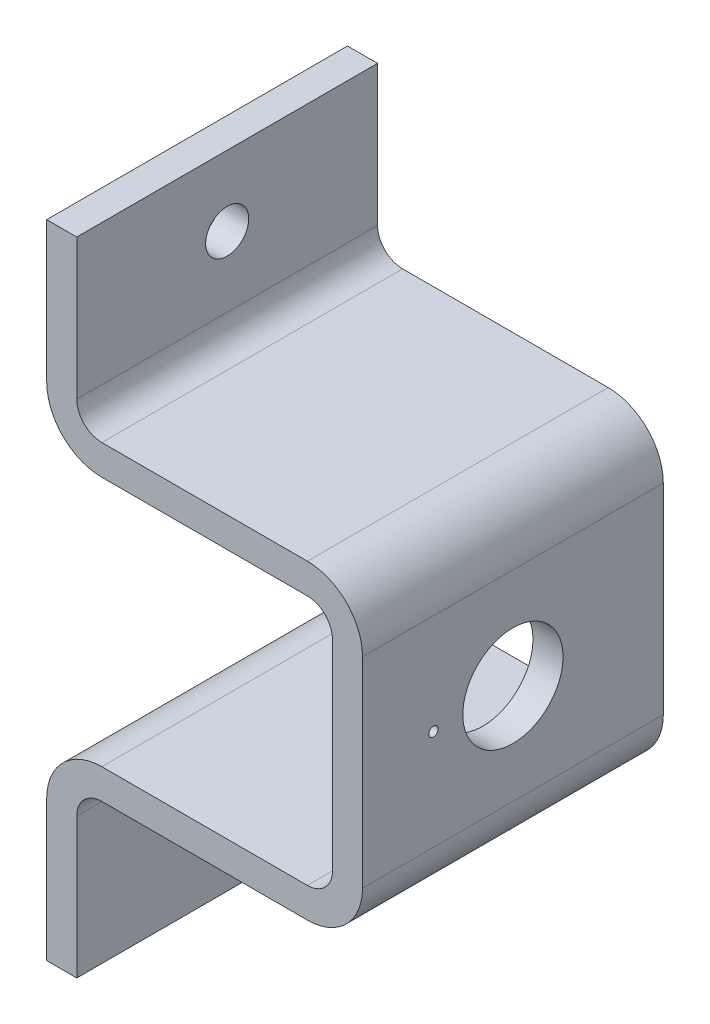
SolidWorks part; units mm, degrees
material "80% - PLA"
ref_plane "Front Plane" through (0, 0, 0) normal (0, 0, 1) x (1, 0, 0)
ref_plane "Top Plane" through (0, 0, 0) normal (0, 1, 0) x (1, 0, 0)
ref_plane "Right Plane" through (0, 0, 0) normal (1, 0, 0) x (0, 0, -1)
sketch "Sketch1" plane through (0, 0, 0) normal (0, 0, 1) x (1, 0, 0)
  line L0 (0, 0) -> (0, 14)
  line L1 (26, 19.5) -> (5.5, 19.5)
  line L2 (28.5, 22) -> (28.5, 42)
  line L3 (26, 44.5) -> (5.5, 44.5)
  line L4 (0, 50) -> (0, 64)
  line L5 (3, 0) -> (3, 14)
  line L6 (5.5, 16.5) -> (26, 16.5)
  line L7 (31.5, 22) -> (31.5, 42)
  line L8 (26, 47.5) -> (5.5, 47.5)
  line L9 (3, 50) -> (3, 64)
  line L10 (0, 0) -> (0, 19.5) construction
  line L11 (0, 19.5) -> (28.5, 19.5) construction
  line L12 (3, 0) -> (3, 16.5) construction
  line L13 (3, 16.5) -> (31.5, 16.5) construction
  line L14 (28.5, 19.5) -> (28.5, 44.5) construction
  line L15 (31.5, 16.5) -> (31.5, 47.5) construction
  line L16 (28.5, 44.5) -> (0, 44.5) construction
  line L17 (31.5, 47.5) -> (3, 47.5) construction
  line L18 (0, 44.5) -> (0, 64) construction
  line L19 (3, 47.5) -> (3, 64) construction
  line L20 (0, 64) -> (3, 64)
  line L21 (3, 0) -> (0, 0)
  arc A0 (0, 14) -> (5.5, 19.5) centre (5.5, 14) cw
  arc A1 (3, 14) -> (5.5, 16.5) centre (5.5, 14) cw
  arc A2 (26, 19.5) -> (28.5, 22) centre (26, 22) ccw
  arc A3 (31.5, 42) -> (26, 47.5) centre (26, 42) ccw
  arc A4 (28.5, 42) -> (26, 44.5) centre (26, 42) ccw
  arc A6 (0, 14) -> (5.5, 19.5) centre (5.5, 14) cw construction
  arc A7 (5.5, 47.5) -> (3, 50) centre (5.5, 50) cw
  arc A8 (5.5, 44.5) -> (0, 50) centre (5.5, 50) cw
  arc A9 (5.5, 44.5) -> (0, 50) centre (5.5, 50) cw construction
  arc A10 (26, 16.5) -> (31.5, 22) centre (26, 22) ccw
  arc A11 (26, 16.5) -> (31.5, 22) centre (26, 22) ccw construction
  arc A12 (31.5, 42) -> (26, 47.5) centre (26, 42) ccw construction
  dimension "D6" = 3
  dimension "D1" = 3
  dimension "D2" = 3
  dimension "D3" = 3
  dimension "D4" = 3
  dimension "D7" = 25.5
  dimension "D8" = 19.5
  dimension "D9" = 19.5
  dimension "D10" = 31
  dimension "D5" = 3
extrude "Boss-Extrude1" add sketch "Sketch1" along normal blind 30
hole_wizard "M4 Clearance Hole1" positions "Sketch3" profile "Sketch2" hole size "M4" standard "ISO"
sketch "Sketch3" plane through (3, 0, 0) normal (1, 0, 0) x (0, 0, -1)
  line L0 (-30, 0) -> (0, 0) construction
  line L1 (0, 0) -> (0, 14) construction
  point P0 (-15, 57)
  point P2 (-15, 7)
  dimension "D1" = 50
  dimension "D2" = 7
  dimension "D3" = 15
sketch "Sketch2" plane through (3, 57, 15) normal (0, 1, 0) x (0, 0, -1)
  line L0 (0, 0) -> (0, 7)
  line L1 (0, 7) -> (2.15, 7)
  line L2 (2.15, 7) -> (2.15, 0)
  line L5 (2.15, 0) -> (0, 0)
  line L10 (0, 7) -> (-2.15, 7) construction
  line L11 (0, -6.35) -> (0, 107.95) construction
  dimension "Hole Dia." = 4.3
  dimension "Hole Depth" = 7
  dimension "Drill Angle" = 180
hole_wizard "M10 Clearance Hole1" positions "Sketch5" profile "Sketch4" hole size "M10" standard "ISO"
sketch "Sketch5" plane through (31.5, 0, 0) normal (1, 0, 0) x (0, 0, -1)
  line L0 (0, 22) -> (0, 42) construction
  line L1 (-30, 42) -> (0, 42) construction
  point P0 (-15, 32)
  dimension "D1" = 15
  dimension "D2" = 10
sketch "Sketch4" plane through (31.5, 32, 15) normal (0, 1, 0) x (0, 0, -1)
  line L0 (0, 0) -> (0, 7)
  line L1 (0, 7) -> (5, 7)
  line L2 (5, 7) -> (5, 0)
  line L5 (5, 0) -> (0, 0)
  line L10 (0, 7) -> (-5, 7) construction
  line L11 (0, -6.35) -> (0, 107.95) construction
  dimension "Hole Dia." = 10
  dimension "Hole Depth" = 7
  dimension "Drill Angle" = 180
sketch "Sketch6" plane through (31.5, 0, 0) normal (1, 0, 0) x (0, 0, -1)
  line L0 (-15, 32) -> (-22.92, 32)
  circle A0 centre (-22.92, 32) radius 0.475
  dimension "D2" = 0.95
  dimension "D1" = 7.92
extrude "Cut-Extrude1" cut sketch "Sketch6" against normal blind 10
